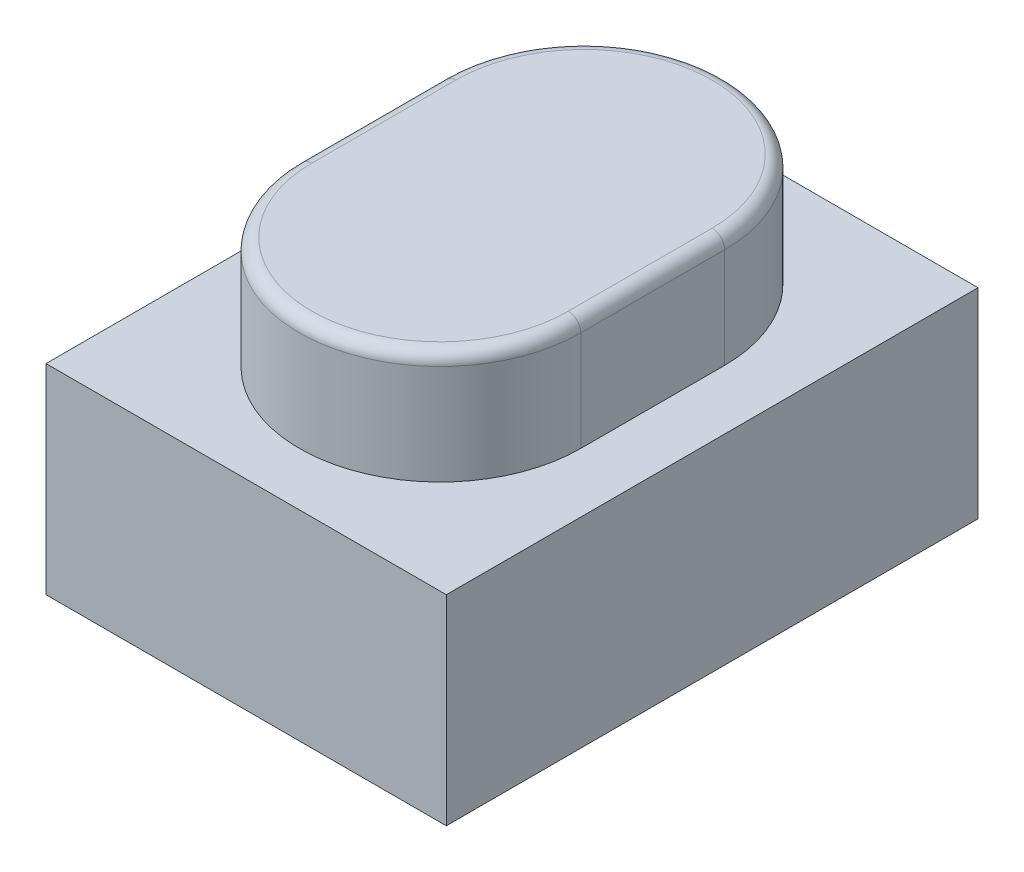
SolidWorks part; units mm, degrees
ref_plane "Front Plane" through (0, 0, 0) normal (0, 0, 1) x (1, 0, 0)
ref_plane "Top Plane" through (0, 0, 0) normal (0, 1, 0) x (1, 0, 0)
ref_plane "Right Plane" through (0, 0, 0) normal (1, 0, 0) x (0, 0, -1)
sketch "BaseS" plane through (0, 0, 0) normal (0, 1, 0) x (1, 0, 0)
  line L1 (-1.6, 2.125) -> (1.6, 2.125)
  line L2 (-1.6, 2.125) -> (-1.6, -2.125)
  line L3 (-1.6, -2.125) -> (1.6, -2.125)
  line L4 (1.6, 2.125) -> (1.6, -2.125)
  line L5 (-1.6, 2.125) -> (1.6, -2.125) construction
  line L6 (-1.6, -2.125) -> (1.6, 2.125) construction
  point P0 (0, 0)
  dimension "Width" = 3.2
  dimension "Length" = 4.25
extrude "Base" add sketch "BaseS" along normal blind 1.6
sketch "ButtonS" plane through (0, 1.6, 0) normal (0, 1, 0) x (1, 0, 0)
  line L0 (0, 0.575) -> (0, -0.575) construction
  line L1 (1.125, 0.575) -> (1.125, -0.575)
  line L2 (-1.125, 0.575) -> (-1.125, -0.575)
  arc A0 (1.125, 0.575) -> (-1.125, 0.575) centre (0, 0.575) ccw
  arc A1 (-1.125, -0.575) -> (1.125, -0.575) centre (0, -0.575) ccw
  point P2 (0, 0)
  dimension "Width" = 2.25
  dimension "Height" = 1.15
extrude "Button" add sketch "ButtonS" along normal blind 0.9
fillet "BF" radius 0.1 4 edges at (1.125, 2.5, 0) (0, 2.5, 1.7) (-1.125, 2.5, 0) (0, 2.5, -1.7)
